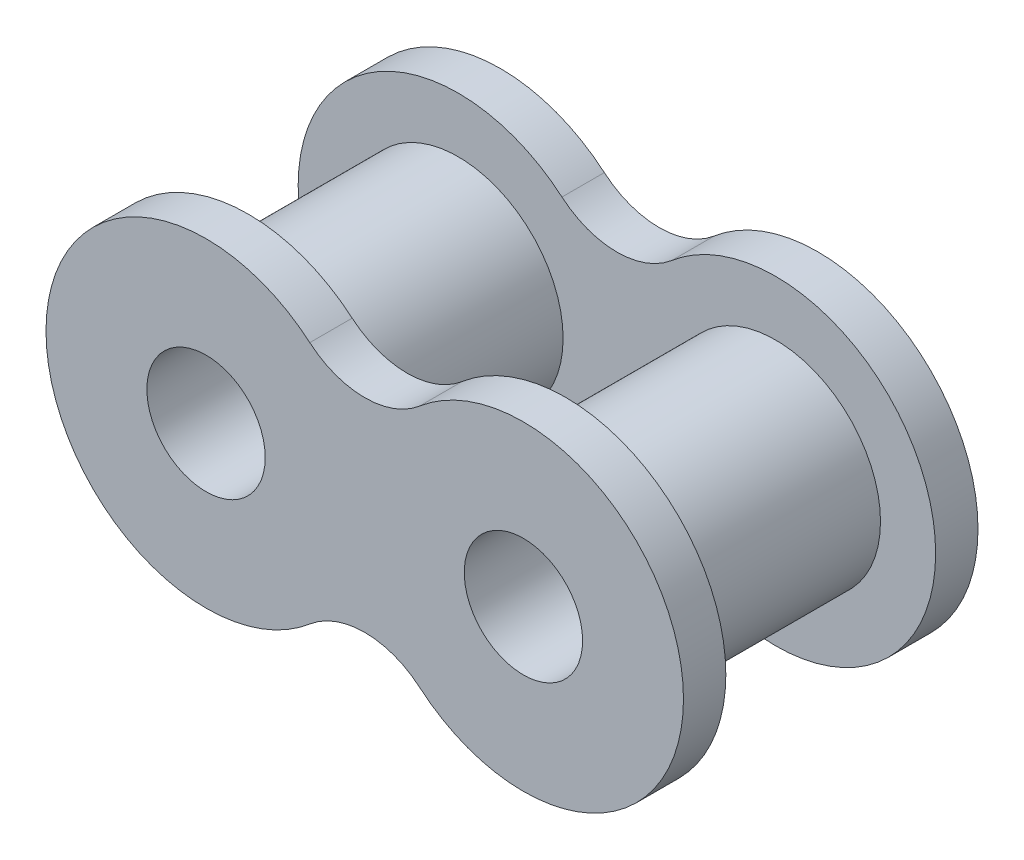
SolidWorks part; units mm, degrees
ref_plane "Front Plane" through (0, 0, 0) normal (0, 0, 1) x (1, 0, 0)
ref_plane "Top Plane" through (0, 0, 0) normal (0, 1, 0) x (1, 0, 0)
ref_plane "Right Plane" through (0, 0, 0) normal (1, 0, 0) x (0, 0, -1)
sketch "Sketch1" plane through (0, 0, 0) normal (0, 0, 1) x (1, 0, 0)
  line L0 (5.9944, 0) -> (-5.9944, 0) construction
  circle A0 centre (-5.9944, 0) radius 3.9624
  circle A1 centre (-5.9944, 0) radius 2.2352
  circle A2 centre (5.9944, 0) radius 2.2352
  circle A3 centre (5.9944, 0) radius 3.9624
  point P3 (6.668, 0)
  point P12 (0, 0)
  dimension "D1" = 7.9248
  dimension "D2" = 4.4704
  dimension "D3" = 11.9888
extrude "Boss-Extrude1" add sketch "Sketch1" along normal mid plane 11.1252
sketch "Sketch2" plane through (0, 0, 5.5626) normal (0, 0, 1) x (1, 0, 0)
  arc A0 (-2.075, 4.6025) -> (-2.075, -4.6025) centre (-5.9944, 0) ccw
  arc A1 (2.075, -4.6025) -> (2.075, 4.6025) centre (5.9944, 0) ccw
  arc A2 (-2.075, 4.6025) -> (2.075, 4.6025) centre (0, 7.0391) ccw
  arc A3 (-2.075, -4.6025) -> (2.075, -4.6025) centre (0, -7.0391) cw
  circle A4 centre (5.9944, 0) radius 3.9624 construction
  circle A5 centre (-5.9944, 0) radius 3.9624 construction
  circle A6 centre (5.9944, 0) radius 3.9624
  circle A7 centre (-5.9944, 0) radius 3.9624
  dimension "D1" = 12.0904
  dimension "D2" = 3.2004
extrude "Boss-Extrude2" add sketch "Sketch2" against normal blind 1.6002
mirror "Mirror1" about plane through (0, 0, 0) normal (0, 0, 1) of "Boss-Extrude2"
